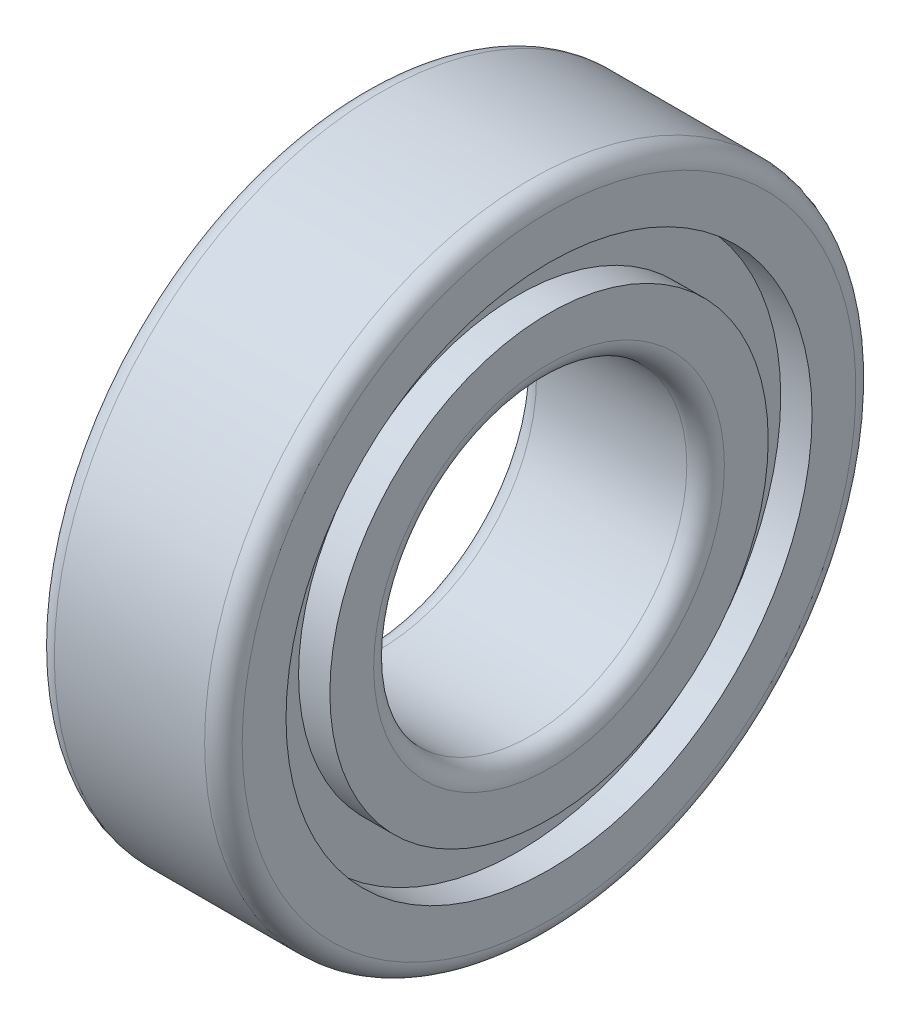
SolidWorks part; units mm, degrees
material "AISI 1020"
ref_plane "Спереди" through (0, 0, 0) normal (0, 0, 1) x (1, 0, 0)
ref_plane "Сверху" through (0, 0, 0) normal (0, 1, 0) x (1, 0, 0)
ref_plane "Справа" through (0, 0, 0) normal (1, 0, 0) x (0, 0, -1)
sketch "Эскиз1" plane through (0, 0, 0) normal (0, 0, 1) x (1, 0, 0)
  line L0 (-1000, 0) -> (49000, 0) construction
  line L1 (0, -1000) -> (0, 49000) construction
  line L2 (6, 12.5) -> (-6, 12.5)
  line L3 (-7.5, 14) -> (-7.5, 17.5)
  line L4 (-7.5, 17.5) -> (-5, 17.5)
  line L5 (-5, 17.5) -> (-5, 21)
  line L6 (-5, 21) -> (-7.5, 21)
  line L7 (-7.5, 21) -> (-7.5, 24.5)
  line L8 (-6, 26) -> (6, 26)
  line L9 (7.5, 21) -> (7.5, 24.5)
  line L10 (5, 21) -> (7.5, 21)
  line L11 (5, 17.5) -> (5, 21)
  line L12 (7.5, 17.5) -> (5, 17.5)
  line L13 (7.5, 14) -> (7.5, 17.5)
  arc A0 (-6, 12.5) -> (-7.5, 14) centre (-6, 14) cw
  arc A1 (-7.5, 24.5) -> (-6, 26) centre (-6, 24.5) cw
  arc A2 (7.5, 24.5) -> (6, 26) centre (6, 24.5) ccw
  arc A3 (6, 12.5) -> (7.5, 14) centre (6, 14) ccw
  point P23 (0, 26)
  point P27 (0, 12.5)
  dimension "_r" = 1.5
  dimension "_d" = 25
  dimension "D" = 52
  dimension "B" = 15
  dimension "D2" = 10
revolve "Повернуть1" add sketch "Эскиз1" angle 360 about L0
other "PropertyManager" [suppressed]
equation "\"D2@Эскиз1\"= \"B@Эскиз1\" / 3 * 2"
